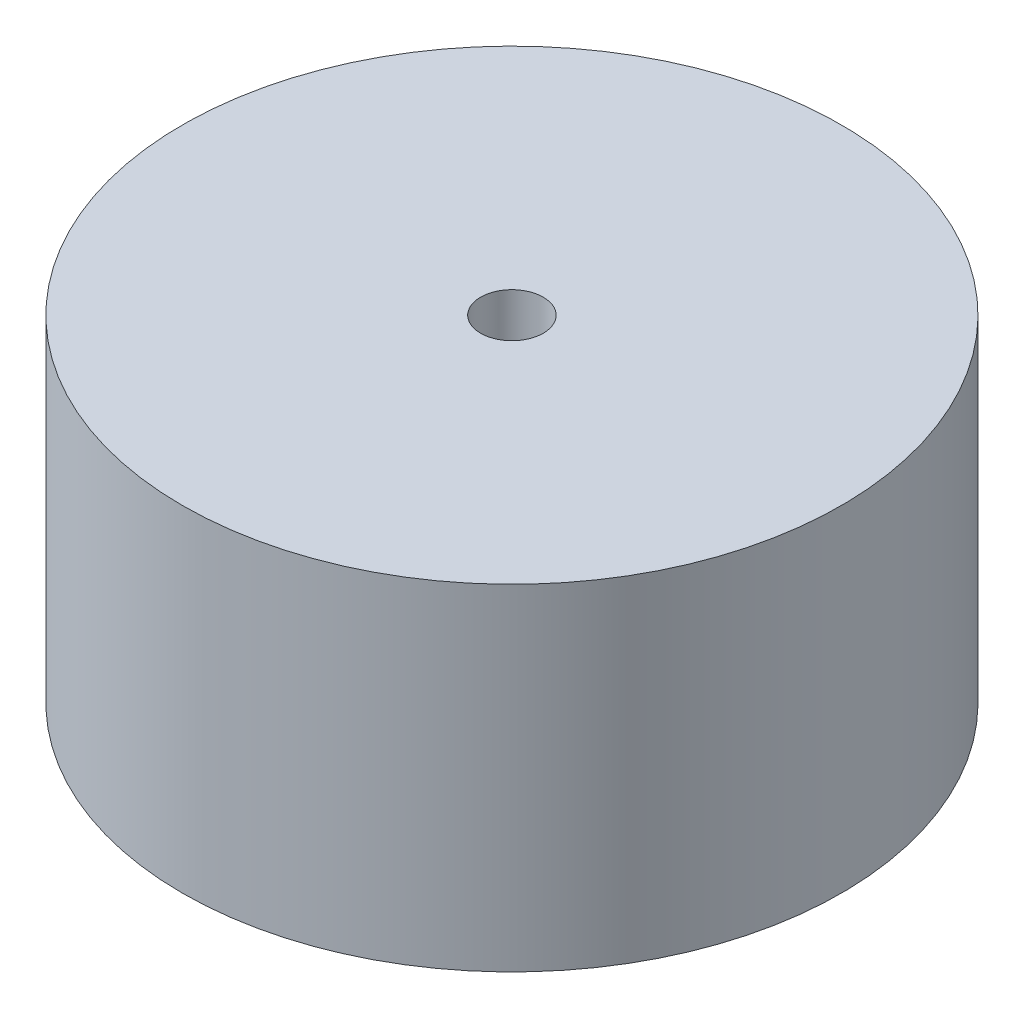
SolidWorks part; units mm, degrees
ref_plane "Front Plane" through (0, 0, 0) normal (0, 0, 1) x (1, 0, 0)
ref_plane "Top Plane" through (0, 0, 0) normal (0, 1, 0) x (1, 0, 0)
ref_plane "Right Plane" through (0, 0, 0) normal (1, 0, 0) x (0, 0, -1)
sketch "Sketch1" plane through (0, 0, 0) normal (0, 1, 0) x (1, 0, 0)
  circle A1 centre (0, 0) radius 17.375
extrude "Boss-Extrude1" add sketch "Sketch1" along normal blind 17.7
sketch "Sketch7" plane through (0, 0, 0) normal (0, -1, 0) x (1, 0, 0)
  circle A0 centre (0, 0) radius 13.545
extrude "Cut-Extrude4" cut sketch "Sketch7" against normal blind 5 contours A0
sketch "Sketch10" plane through (0, 5, 0) normal (0, -1, 0) x (1, 0, 0)
  circle A0 centre (0, 0) radius 3.485
extrude "Boss-Extrude3" add sketch "Sketch10" along normal blind 1 contours A0
sketch "Sketch11" plane through (0, 4, 0) normal (0, -1, 0) x (1, 0, 0)
  circle A3 centre (0, 0) radius 1.65
sketch "Sketch14" plane through (0, 5, 0) normal (0, -1, 0) x (1, 0, 0)
  point P10 (0, 0)
extrude "Cut-Extrude5" cut sketch "Sketch11" against normal up to surface (13.7 mm away) up to face at (0, 17.7, 17.375)
sketch "Sketch16" plane through (0, 5, 0) normal (0, -1, 0) x (-1, 0, 0)
  line L0 (-2.4643, -2.4643) -> (-9.5778, -9.5778) construction
  line L1 (0, -13.545) -> (0, -3.485) construction
  line L2 (0, 3.485) -> (0, 13.545) construction
  line L3 (-13.545, 0) -> (-3.485, 0) construction
  line L4 (-9.5778, 9.5778) -> (-2.4643, 2.4643) construction
  line L5 (9.5778, 9.5778) -> (2.4643, 2.4643) construction
  line L6 (13.545, 0) -> (3.485, 0) construction
  line L7 (2.4643, -2.4643) -> (9.5778, -9.5778) construction
  circle A1 centre (0, 0) radius 13.545 construction
  circle A2 centre (0, 0) radius 3.485 construction
